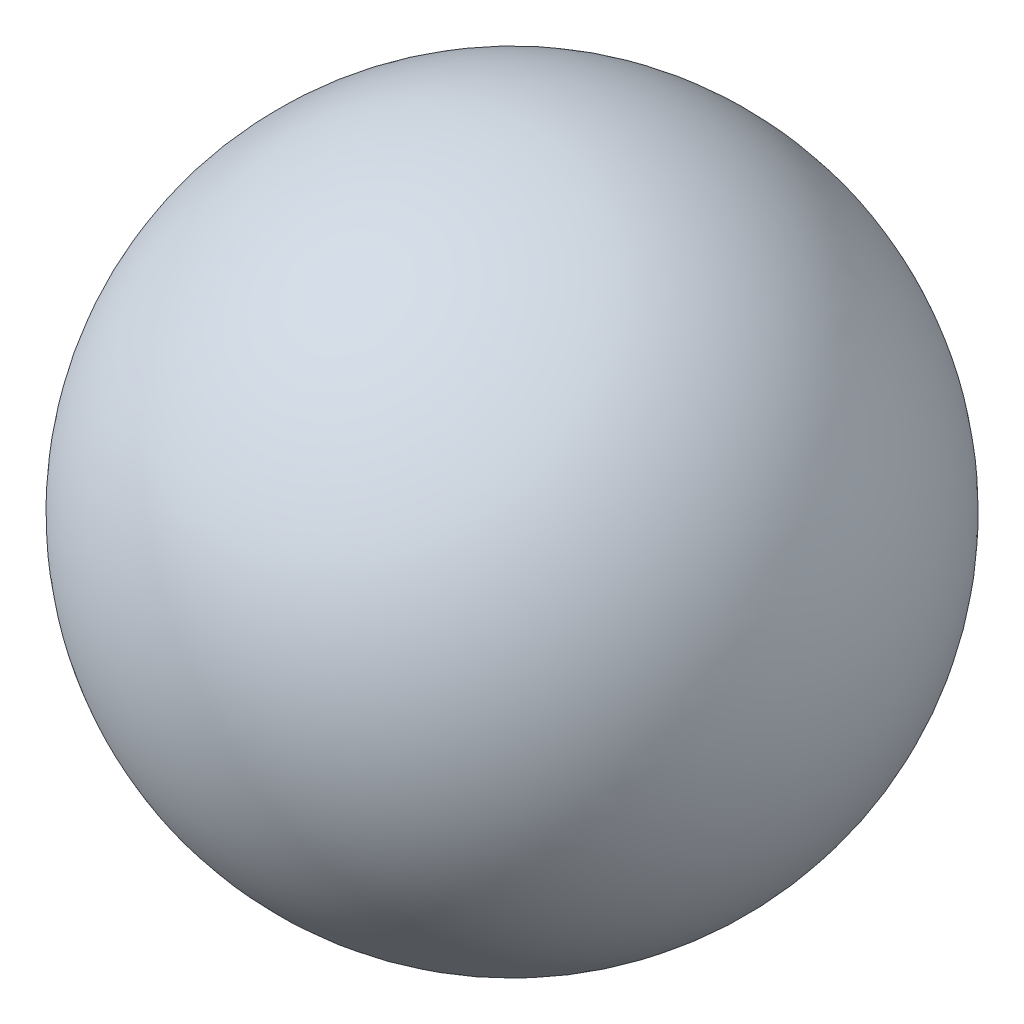
SolidWorks part; units mm, degrees
ref_plane "Front Plane" through (0, 0, 0) normal (0, 0, 1) x (1, 0, 0)
ref_plane "Top Plane" through (0, 0, 0) normal (0, 1, 0) x (1, 0, 0)
ref_plane "Right Plane" through (0, 0, 0) normal (1, 0, 0) x (0, 0, -1)
sketch "Sketch1" plane through (0, 0, 0) normal (0, 1, 0) x (1, 0, 0)
  line L0 (0, 0) -> (0, 49)
  arc A0 (0, 49) -> (0, 0) centre (0, 24.5) ccw
  dimension "D1" = 49
revolve "Revolve1" add sketch "Sketch1" angle 360 about L0
